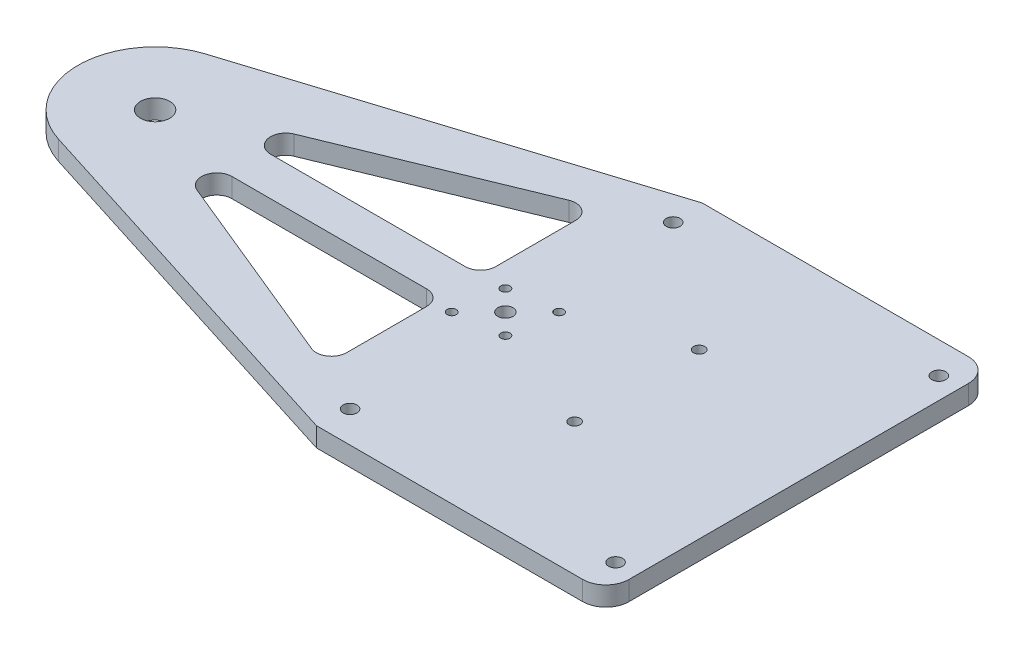
SolidWorks part; units mm, degrees
material "UHMW"
ref_plane "Front Plane" through (0, 0, 0) normal (0, 0, 1) x (1, 0, 0)
ref_plane "Top Plane" through (0, 0, 0) normal (0, 1, 0) x (1, 0, 0)
ref_plane "Right Plane" through (0, 0, 0) normal (1, 0, 0) x (0, 0, -1)
sketch "Sketch1" plane through (0, 0, 0) normal (0, 1, 0) x (1, 0, 0)
  line L0 (-47.625, 0) -> (47.625, 0) construction
  line L1 (-47.625, -63.5) -> (47.625, -63.5)
  line L2 (-47.625, -63.5) -> (-47.625, 63.5)
  line L3 (-47.625, 63.5) -> (47.625, 63.5)
  line L4 (47.625, -63.5) -> (47.625, 63.5)
  line L5 (-47.625, -63.5) -> (47.625, 63.5) construction
  line L6 (-47.625, 63.5) -> (47.625, -63.5) construction
  point P0 (0, 0)
  dimension "D1" = 95.25
  dimension "D2" = 127
  dimension "D3" = 63.5
extrude "Boss-Extrude1" add sketch "Sketch1" along normal blind 6.35
sketch "Sketch4" plane through (0, 6.35, 0) normal (0, 1, 0) x (1, 0, 0)
  line L1 (-47.625, 63.5) -> (-171.916, 24.2193)
  line L5 (-47.625, 63.5) -> (-47.625, -63.5) construction
  line L9 (-47.625, -63.5) -> (-171.916, -24.2193)
  line L10 (-47.625, 63.5) -> (-47.625, -63.5)
  arc A0 (-171.916, 24.2193) -> (-171.916, -24.2193) centre (-164.2618, 0) ccw
  circle A1 centre (-48.9458, 0) radius 2.5 construction
  dimension "D1" = 50.8
  dimension "D2" = 115.316
extrude "Boss-Extrude3" add sketch "Sketch4" against normal blind 6.35
sketch "Sketch5" plane through (0, 6.35, 0) normal (0, 1, 0) x (1, 0, 0)
  line L0 (-48.9458, 0) -> (-31.7264, 0) construction
  line L3 (-48.9458, 0) -> (-91.3931, 0) construction
  circle A0 centre (-164.2618, 0) radius 4.826
  circle A1 centre (-48.9458, 0) radius 2.5
  arc A2 (-171.916, 24.2193) -> (-171.916, -24.2193) centre (-164.2618, 0) ccw construction
  arc A3 (-171.916, 24.2193) -> (-171.916, -24.2193) centre (-164.2618, 0) ccw
  circle A4 centre (-42.2283, -6.7175) radius 1.5
  circle A5 centre (-40.107, 8.8388) radius 1.5
  circle A6 centre (-57.7846, -8.8388) radius 1.5
  circle A7 centre (-55.6633, 6.7175) radius 1.5
  circle A8 centre (-40.107, 8.8388) radius 1.5 construction
  circle A9 centre (-55.6633, 6.7175) radius 1.5 construction
  circle A10 centre (-57.7846, -8.8388) radius 1.5 construction
  circle A11 centre (-42.2283, -6.7175) radius 1.5 construction
  circle A12 centre (-48.9458, 0) radius 2.5 construction
  point P20 (-48.9458, 0)
  dimension "D1" = 9.652
extrude "Cut-Extrude1" cut sketch "Sketch5" against normal through all contours A0 | A1 | A5 | A6 | A7 | A4
sketch "Sketch6" plane through (0, 6.35, 0) normal (0, 1, 0) x (1, 0, 0)
  line L0 (-63.5, 6.35) -> (-63.5, -6.35) construction
  line L1 (-63.5, 45.1637) -> (-157.9118, 6.35)
  line L2 (-157.9118, 6.35) -> (-63.5, 6.35)
  line L3 (-63.5, 6.35) -> (-63.5, 45.1637)
  line L4 (-63.5, -6.35) -> (-63.5, -45.1637)
  line L5 (-63.5, -45.1637) -> (-157.9118, -6.35)
  line L6 (-157.9118, -6.35) -> (-63.5, -6.35)
  line L7 (0, 0) -> (-63.5, 0) construction
  line L8 (-189.6618, 75.5498) -> (-189.6618, -75.5498) construction
  line L9 (-47.625, 63.5) -> (-171.916, 24.2193) construction
  arc A0 (-171.916, 24.2193) -> (-171.916, -24.2193) centre (-164.2618, 0) ccw construction
  point P12 (-189.6618, 0)
  dimension "D1" = 31.75
  dimension "D2" = 12.7
  dimension "D3" = 12.7
  dimension "D4" = 63.5
extrude "Cut-Extrude2" cut sketch "Sketch6" against normal through all
fillet "Fillet9" radius 5 6 edges at (-157.9118, 3.175, 6.35) (-63.5, 3.175, 6.35) (-63.5, 3.175, 45.1637) (-63.5, 3.175, -6.35) (-157.9118, 3.175, -6.35) (-63.5, 3.175, -45.1637)
fillet "Fillet10" radius 7.62 2 edges at (47.625, 3.175, -63.5) (47.625, 3.175, 63.5)
sketch "Sketch7" plane through (0, 6.35, 0) normal (0, 1, 0) x (1, 0, 0)
  circle A0 centre (-46.8896, -53.2002) radius 2.2812
  circle A1 centre (-46.8896, 53.1801) radius 2.2812
  circle A2 centre (40.557, 53.1902) radius 2.2812
  circle A3 centre (40.5396, -53.2204) radius 2.2812
  circle A4 centre (-46.8896, 53.1801) radius 2.2812 construction
  circle A5 centre (40.557, 53.1902) radius 2.2812 construction
  circle A6 centre (40.5396, -53.2204) radius 2.2812 construction
  circle A7 centre (-46.8896, -53.2002) radius 2.2812 construction
extrude "Cut-Extrude3" cut sketch "Sketch7" against normal through all
sketch "Sketch8" plane through (0, 6.35, 0) normal (0, 1, 0) x (1, 0, 0)
  circle A0 centre (-6.3285, -19.8289) radius 1.83
  circle A1 centre (-6.3283, 21.1715) radius 1.83
  circle A2 centre (-6.3285, -19.8289) radius 1.83 construction
  circle A3 centre (-6.3283, 21.1715) radius 1.83 construction
extrude "Cut-Extrude4" cut sketch "Sketch8" against normal through all
